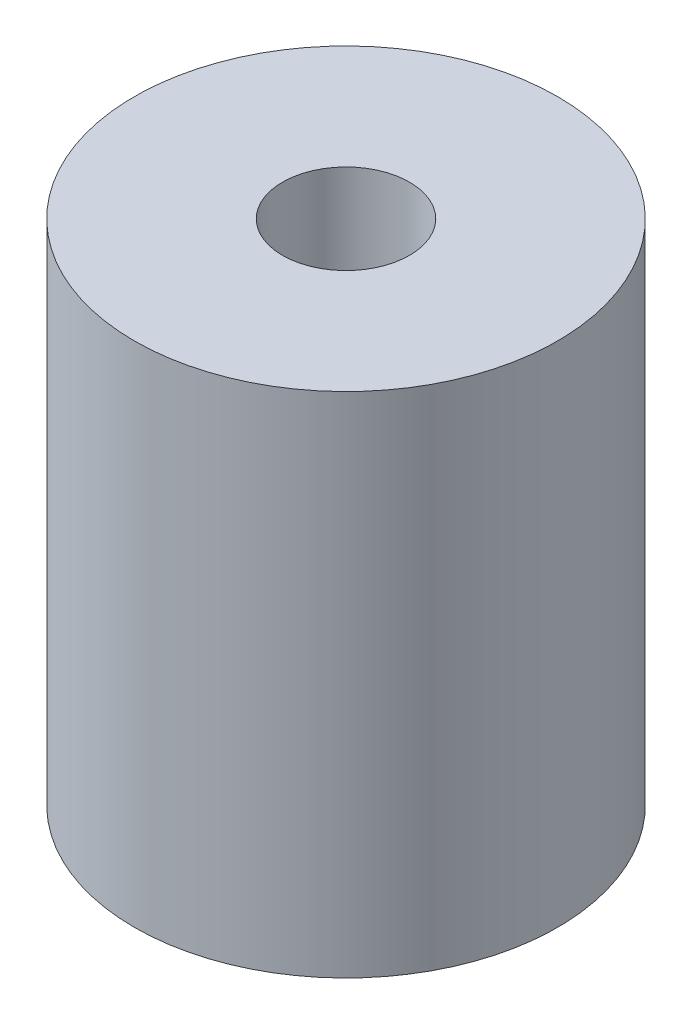
SolidWorks part; units mm, degrees
ref_plane "前视基准面" through (0, 0, 0) normal (0, 0, 1) x (1, 0, 0)
ref_plane "上视基准面" through (0, 0, 0) normal (0, 1, 0) x (1, 0, 0)
ref_plane "右视基准面" through (0, 0, 0) normal (1, 0, 0) x (0, 0, -1)
sketch "草图1" plane through (0, 0, 0) normal (0, 1, 0) x (1, 0, 0)
  circle A0 centre (0, 0) radius 5
  circle A1 centre (0, 0) radius 1.5
  dimension "D1" = 10
  dimension "D2" = 3
extrude "凸台-拉伸1" add sketch "草图1" along normal blind 12
